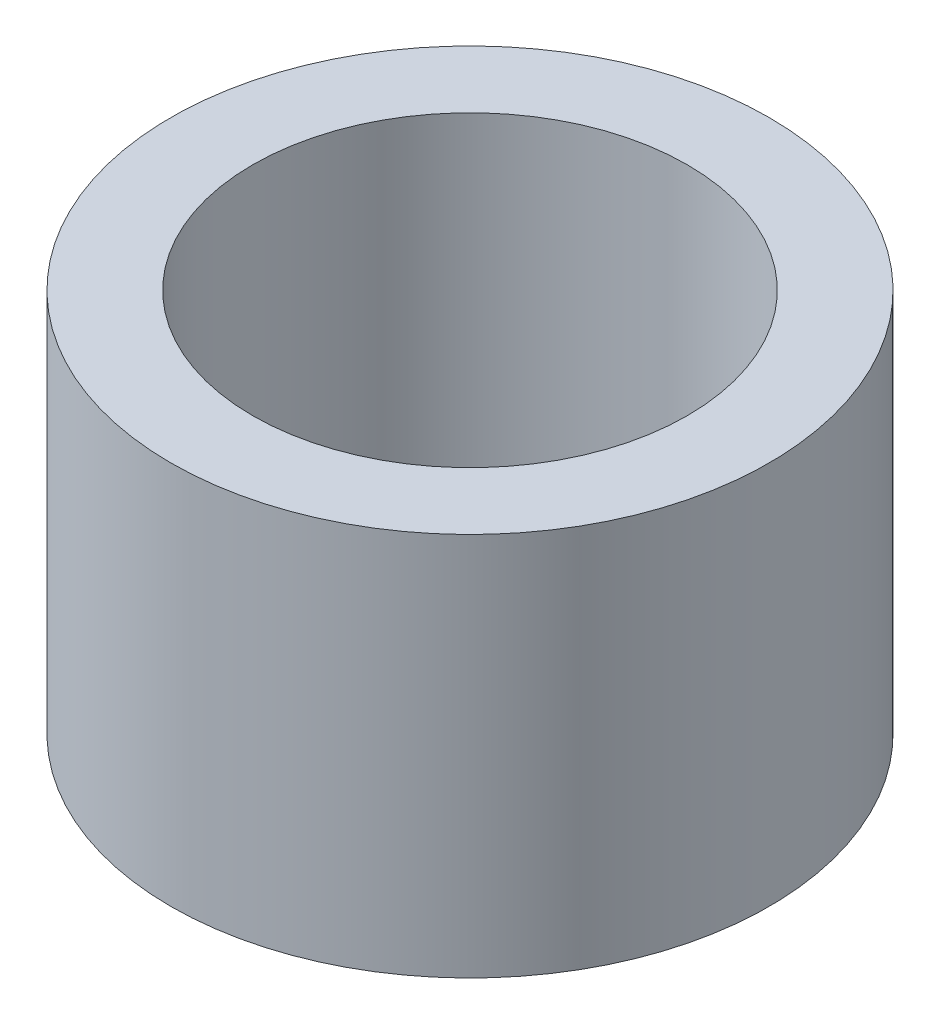
SolidWorks part; units mm, degrees
material "Rubber"
ref_plane "Front Plane" through (0, 0, 0) normal (0, 0, 1) x (1, 0, 0)
ref_plane "Top Plane" through (0, 0, 0) normal (0, 1, 0) x (1, 0, 0)
ref_plane "Right Plane" through (0, 0, 0) normal (1, 0, 0) x (0, 0, -1)
sketch "Sketch1" plane through (0, 0, 0) normal (0, 1, 0) x (1, 0, 0)
  circle A0 centre (0, 0) radius 4.515
  circle A1 centre (0, 0) radius 6.215
  dimension "D1" = 9.03
  dimension "D2" = 1.7
extrude "Boss-Extrude3" add sketch "Sketch1" along normal blind 7.98
